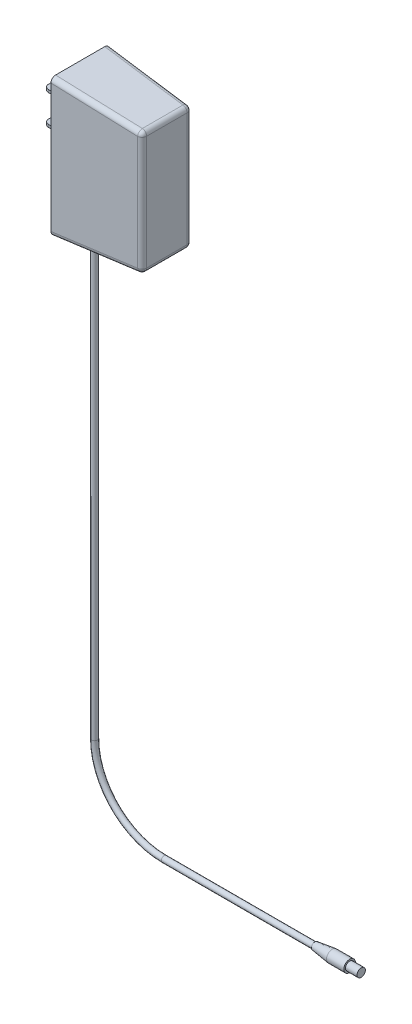
SolidWorks part; units mm, degrees
material "ABS"
ref_plane "Front Plane" through (0, 0, 0) normal (0, 0, 1) x (1, 0, 0)
ref_plane "Top Plane" through (0, 0, 0) normal (0, 1, 0) x (1, 0, 0)
ref_plane "Right Plane" through (0, 0, 0) normal (1, 0, 0) x (0, 0, -1)
sketch "Sketch1" plane through (0, 0, 0) normal (0, 0, 1) x (1, 0, 0)
  line L0 (0, 0) -> (-101.6, 0)
  line L1 (-139.7, 38.1) -> (-139.7, 355.6)
  arc A0 (-101.6, 0) -> (-139.7, 38.1) centre (-101.6, 38.1) cw
  point P6 (-139.7, 0)
  dimension "D3" = 38.1
  dimension "D1" = 355.6
  dimension "D2" = 139.7
sketch "Sketch2" plane through (0, 0, 0) normal (1, 0, 0) x (0, 0, -1)
  circle A0 centre (0, 0) radius 1.5875
  dimension "D1" = 3.175
sweep "Sweep1" add profiles "Sketch2" path "Sketch1"
sketch "Sketch3" plane through (0, 0, 0) normal (1, 0, 0) x (0, 0, -1)
  circle A0 centre (0, 0) radius 3.175
  dimension "D1" = 6.35
extrude "Boss-Extrude1" add sketch "Sketch3" against normal blind 19.05
sketch "Sketch4" plane through (0, 0, 0) normal (1, 0, 0) x (0, 0, -1)
  circle A0 centre (0, 0) radius 2.286
  dimension "D1" = 4.572
extrude "Boss-Extrude2" add sketch "Sketch4" along normal blind 6.35
chamfer "Chamfer1" distance 1.27 distance2 9.525 1 edges at (-19.05, 0, -3.175)
sketch "Sketch5" plane through (0, 0, 0) normal (0, 0, 1) x (1, 0, 0)
  line L0 (-100.1375, 355.6) -> (-147.6375, 355.6)
  line L1 (-147.6375, 355.6) -> (-147.6375, 280.1)
  line L2 (-147.6375, 280.1) -> (-100.1375, 280.1)
  line L4 (-100.1375, 280.1) -> (-100.1375, 355.6)
  line L5 (-138.1125, 355.6) -> (-141.2875, 355.6) construction
  line L6 (-141.2875, 355.6) -> (-141.2875, 38.1) construction
  dimension "D1" = 47.5
  dimension "D2" = 75.5
  dimension "D3" = 6.35
extrude "Boss-Extrude3" add sketch "Sketch5" along normal mid plane 32
sketch "Sketch6" plane through (-147.6375, 0, 0) normal (1, 0, 0) x (0, 0, -1)
  line L0 (0, 107.3971) -> (0, -107.3971) construction
  line L1 (-4, 335.8) -> (4, 335.8)
  line L2 (-4, 335.8) -> (-4, 337.3)
  line L3 (-4, 337.3) -> (4, 337.3)
  line L4 (4, 335.8) -> (4, 337.3)
  line L5 (-4, 335.8) -> (4, 337.3) construction
  line L6 (-4, 337.3) -> (4, 335.8) construction
  line L7 (-16, 355.6) -> (16, 355.6) construction
  line L8 (-4, 319.29) -> (4, 319.29)
  line L9 (-4, 319.29) -> (-4, 320.79)
  line L10 (-4, 320.79) -> (4, 320.79)
  line L11 (4, 319.29) -> (4, 320.79)
  line L12 (-4, 319.29) -> (4, 320.79) construction
  line L13 (-4, 320.79) -> (4, 319.29) construction
  point P0 (0, 336.55)
  point P7 (0, 320.04)
  dimension "D1" = 16.51
  dimension "D2" = 8
  dimension "D3" = 1.5
  dimension "D4" = 19.05
extrude "Boss-Extrude4" add sketch "Sketch6" against normal blind 15.88
draft "Draft1" type of draft neutral plane draft angle 5 faces to draft 2 face at (-123.8875, 280.1, 0) face at (-123.8875, 355.6, 0) neutral plane through (-147.6375, 355.6, 16) neutral plane normal (-1, 0, 0) reverse direction yes parameters "D1"=5
draft "Draft2" type of draft neutral plane draft angle 3 faces to draft 2 face at (-123.8875, 317.85, -16) face at (-123.8875, 317.85, 16) neutral plane through (-147.6375, 355.6, 16) neutral plane normal (-1, 0, 0) reverse direction yes parameters "D1"=3
fillet "Fillet1" radius 2.54 8 edges at (-123.8875, 282.1779, 14.7553) (-123.8875, 282.1779, -14.7553) (-123.8875, 353.5221, -14.7553) (-123.8875, 353.5221, 14.7553) (-100.1375, 284.2557, 0) (-100.1375, 317.85, 13.5106) (-100.1375, 351.4443, 0) (-100.1375, 317.85, -13.5106)
fillet "Fillet2" radius 2.54 4 edges at (-163.5175, 320.04, 4) (-163.5175, 320.04, -4) (-163.5175, 336.55, -4) (-163.5175, 336.55, 4)
